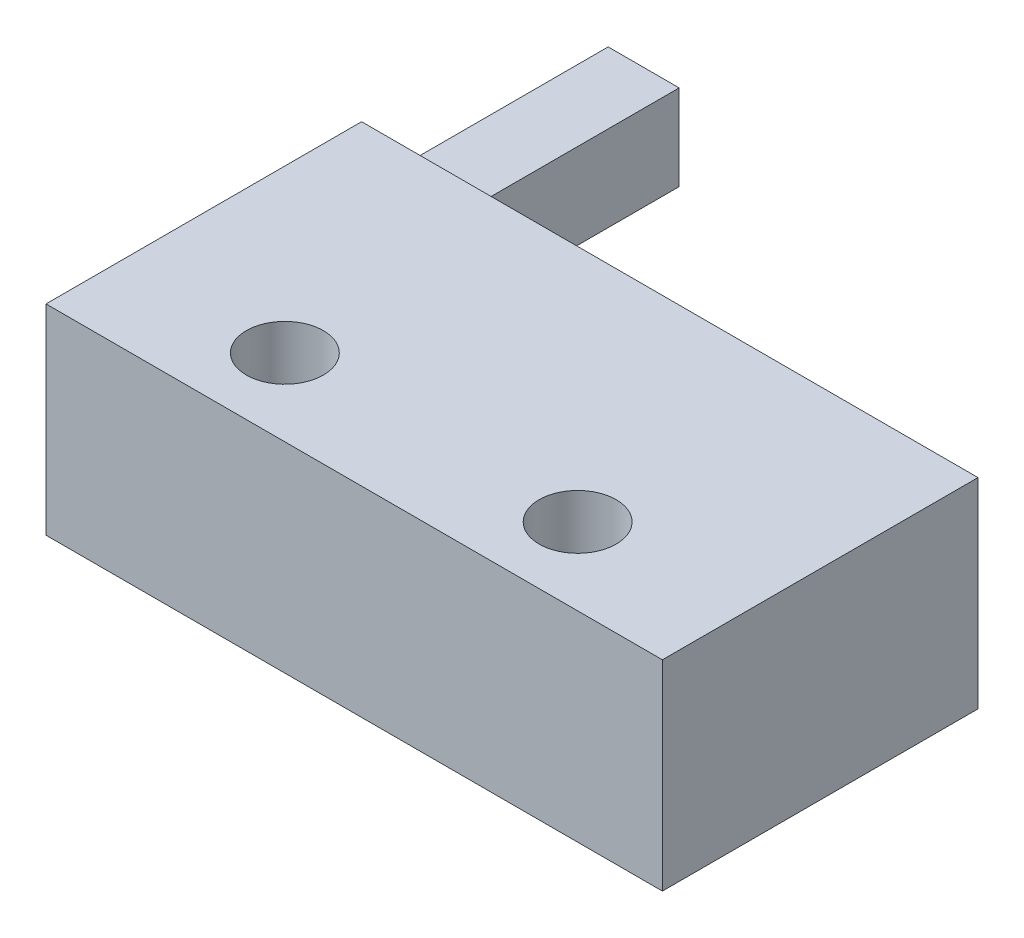
SolidWorks part; units mm, degrees
ref_plane "前视基准面" through (0, 0, 0) normal (0, 0, 1) x (1, 0, 0)
ref_plane "上视基准面" through (0, 0, 0) normal (0, 1, 0) x (1, 0, 0)
ref_plane "右视基准面" through (0, 0, 0) normal (1, 0, 0) x (0, 0, -1)
sketch "草图1" plane through (0, 0, 0) normal (0, 1, 0) x (1, 0, 0)
  line L1 (-10, 5.12) -> (10, 5.12)
  line L2 (-10, 5.12) -> (-10, -5.12)
  line L3 (-10, -5.12) -> (10, -5.12)
  line L4 (10, 5.12) -> (10, -5.12)
  line L5 (-10, 5.12) -> (10, -5.12) construction
  line L6 (-10, -5.12) -> (10, 5.12) construction
  point P0 (0, 0)
  dimension "D1" = 20
  dimension "D2" = 10.24
extrude "凸台-拉伸1" add sketch "草图1" along normal blind 6.5
sketch "草图2" plane through (0, 6.5, 0) normal (0, 1, 0) x (1, 0, 0)
  line L0 (0, 0) -> (0, -6.3976) construction
  line L1 (-10, -5.12) -> (10, -5.12) construction
  circle A0 centre (-4.75, -2.62) radius 1.25
  circle A2 centre (4.75, -2.62) radius 1.25
  point P7 (0, 0)
  dimension "D1" = 2.5
  dimension "D2" = 2.5
  dimension "D3" = 9.5
extrude "切除-拉伸1" cut sketch "草图2" against normal through all
sketch "草图4" plane through (0, 0, -5.12) normal (0, 0, -1) x (-1, 0, 0)
  line L0 (10, 6.5) -> (10, 0) construction
  line L1 (7.6964, 4.6018) -> (10, 4.6018)
  line L2 (7.6964, 4.6018) -> (7.6964, 1.8259)
  line L3 (7.6964, 1.8259) -> (10, 1.8259)
  line L4 (10, 4.6018) -> (10, 1.8259)
  line L5 (7.6964, 4.6018) -> (10, 1.8259) construction
  line L6 (7.6964, 1.8259) -> (10, 4.6018) construction
  point P0 (8.8482, 3.2139)
extrude "凸台-拉伸2" add sketch "草图4" along normal blind 8
